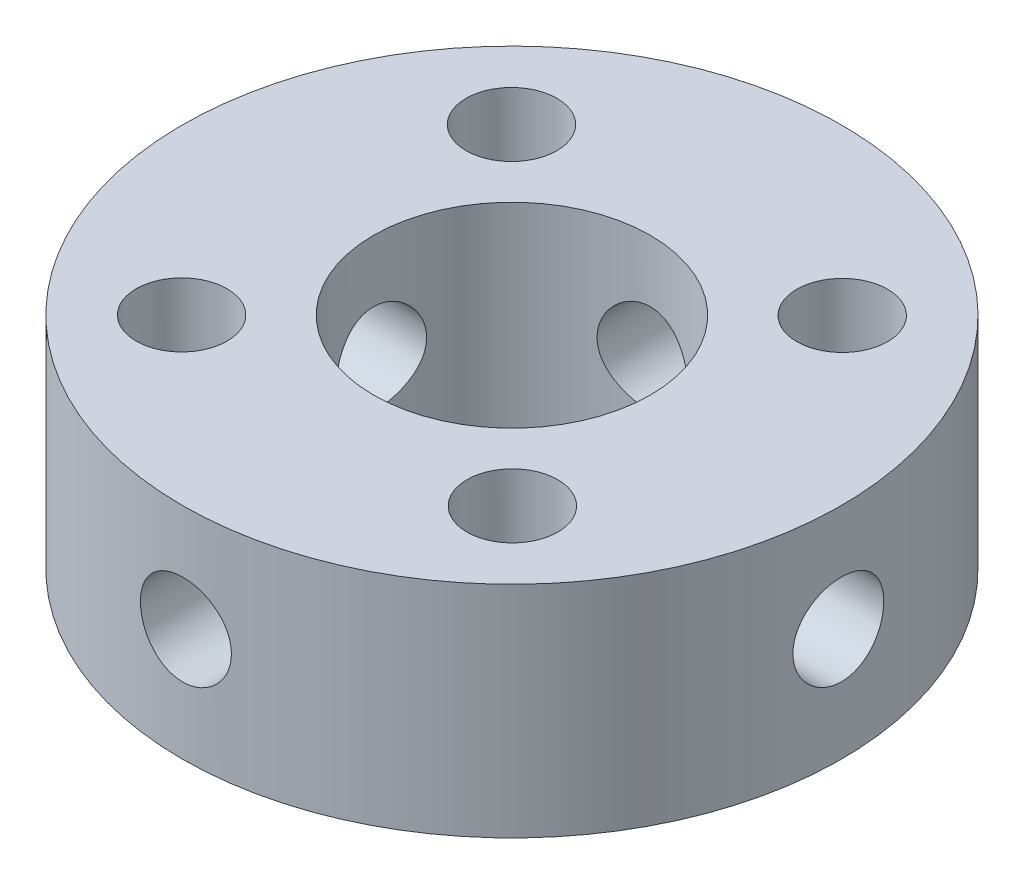
SolidWorks part; units mm, degrees
ref_plane "Front Plane" through (0, 0, 0) normal (0, 0, 1) x (1, 0, 0)
ref_plane "Top Plane" through (0, 0, 0) normal (0, 1, 0) x (1, 0, 0)
ref_plane "Right Plane" through (0, 0, 0) normal (1, 0, 0) x (0, 0, -1)
sketch "Sketch1" plane through (0, 0, 0) normal (0, 1, 0) x (1, 0, 0)
  circle A0 centre (0, 0) radius 16
  circle A1 centre (0, 0) radius 38.1
  dimension "D1" = 76.2
extrude "Boss-Extrude1" add sketch "Sketch1" along normal blind 25.4
hole_wizard "Ø10.5 (10.5) Diameter Hole1" positions "3DSketch1" profile "Sketch2" hole size "Ø10.5" standard "Ansi Metric"
sketch3d "3DSketch1"
  line L2 (19.1178, 0, -19.0659) -> (19.1178, 0, 19.0659)
  line L3 (19.1178, 0, -19.0659) -> (-19.1178, 0, -19.0659)
  line L4 (-19.1178, 0, -19.0659) -> (-19.1178, 0, 19.0659)
  line L5 (19.1178, 0, 19.0659) -> (-19.1178, 0, 19.0659)
  line L6 (19.1178, 0, -19.0659) -> (-19.1178, 0, 19.0659) construction
  line L7 (-19.1178, 0, -19.0659) -> (19.1178, 0, 19.0659) construction
  line L8 (0, 0, 0) -> (-0.0501, 0, -38.1)
  line L9 (-0.0501, 0, -38.1) -> (-0.0501, 13, -38.1)
  line L11 (0, 0, 0) -> (-38.1, 0, 0)
  line L12 (-38.1, 0, 0) -> (-38.1, 13, 0)
  circle A0 centre (0, 0, 0) radius 27
  circle A1 centre (0, 0, 0) radius 38.1 construction
  point P0 (-0.0501, 13, -38.1)
  point P1 (-38.1, 13, 0)
  point P3 (19.1178, 0, -19.0659)
  point P5 (-19.1178, 0, -19.0659)
  point P7 (-19.1178, 0, 19.0659)
  point P9 (19.1178, 0, 19.0659)
  point P252 (0, 27, 0)
  point P457 (0, 38.1, 0)
  dimension "D1" = 13
  dimension "D2" = 13
sketch "Sketch2" plane through (-0.0501, 13, -38.1) normal (0, 1, 0) x (-1, 0, 0.0013)
  line L0 (0, 0) -> (0, 303.1545)
  line L1 (0, 303.1545) -> (5.25, 300)
  line L2 (5.25, 300) -> (5.25, 0)
  line L5 (5.25, 0) -> (0, 0)
  line L10 (0, 303.1545) -> (-5.25, 300) construction
  line L11 (0, -6.35) -> (0, 107.95) construction
  dimension "Hole Dia." = 10.5
  dimension "Hole Depth" = 300
  dimension "Drill Angle" = 118
